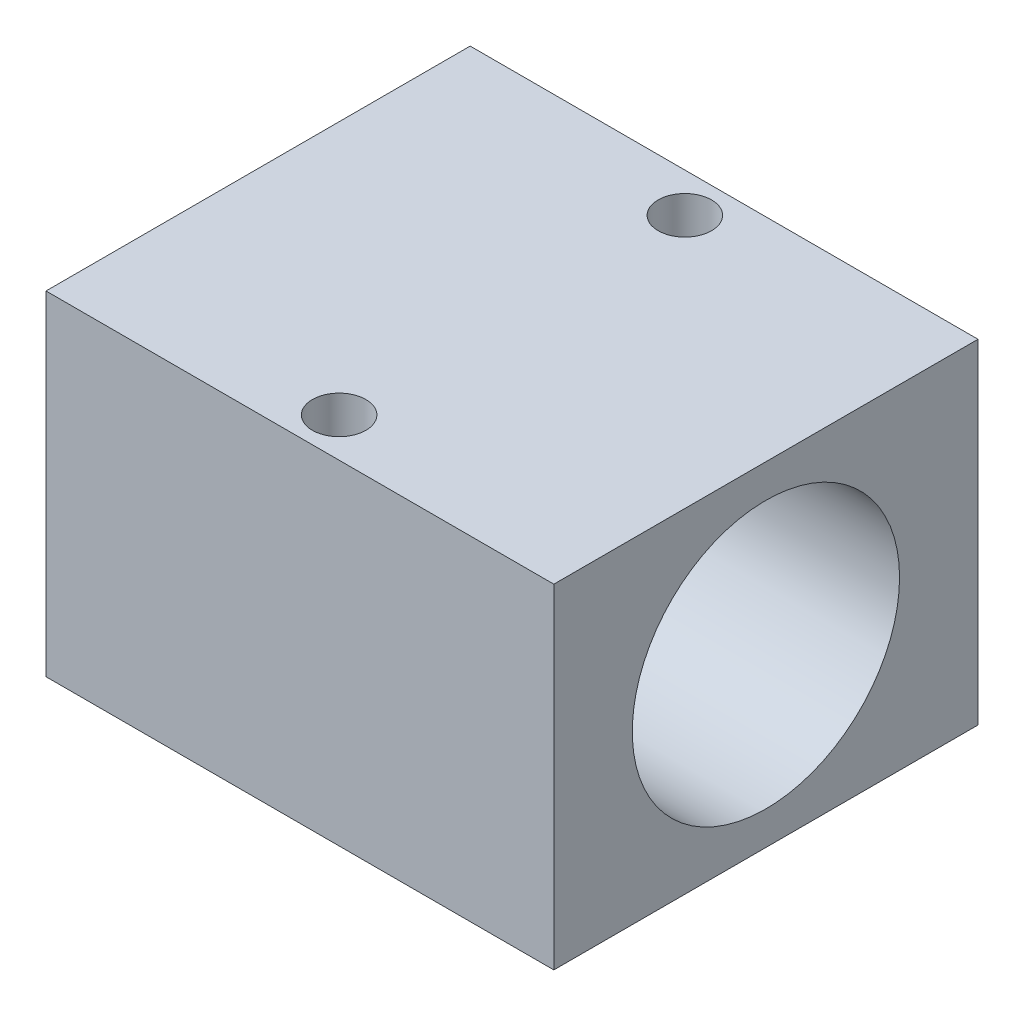
SolidWorks part; units mm, degrees
ref_plane "Front Plane" through (0, 0, 0) normal (0, 0, 1) x (1, 0, 0)
ref_plane "Top Plane" through (0, 0, 0) normal (0, 1, 0) x (1, 0, 0)
ref_plane "Right Plane" through (0, 0, 0) normal (1, 0, 0) x (0, 0, -1)
sketch "Sketch1" plane through (0, 0, 0) normal (0, 1, 0) x (1, 0, 0)
  line L0 (-9.5, 7.935) -> (9.5, -7.935) construction
  line L1 (-9.5, -7.935) -> (9.5, -7.935)
  line L2 (-9.5, -7.935) -> (-9.5, 7.935)
  line L3 (-9.5, 7.935) -> (9.5, 7.935)
  line L4 (9.5, -7.935) -> (9.5, 7.935)
  point P4 (0, 0)
  dimension "D1" = 15.87
  dimension "D2" = 19
extrude "Extrude1" add sketch "Sketch1" along normal blind 12.5
sketch "Sketch2" plane through (9.5, 0, 0) normal (1, 0, 0) x (0, 0, -1)
  line L0 (-7.935, 12.5) -> (7.935, 0) construction
  line L1 (-7.935, 0) -> (7.935, 0) construction
  line L2 (7.935, 12.5) -> (7.935, 0) construction
  circle A0 centre (0, 6.25) radius 5
  point P9 (0, 6.25)
  dimension "D1" = 10
extrude "Cut-Extrude1" cut sketch "Sketch2" against normal blind 22.5
sketch "Sketch3" plane through (0, 12.5, 0) normal (0, 1, 0) x (1, 0, 0)
  line L0 (-9.5, -7.935) -> (-9.5, -5) construction
  line L1 (-9.5, 7.935) -> (-9.5, -7.935) construction
  line L2 (0, 0) -> (14.5422, 0) construction
  circle A0 centre (0, -6.4675) radius 1
  circle A1 centre (0, 6.4675) radius 1
  point P9 (-9.5, -6.4675)
  dimension "D1" = 2
extrude "Cut-Extrude2" cut sketch "Sketch3" against normal blind 22.5
